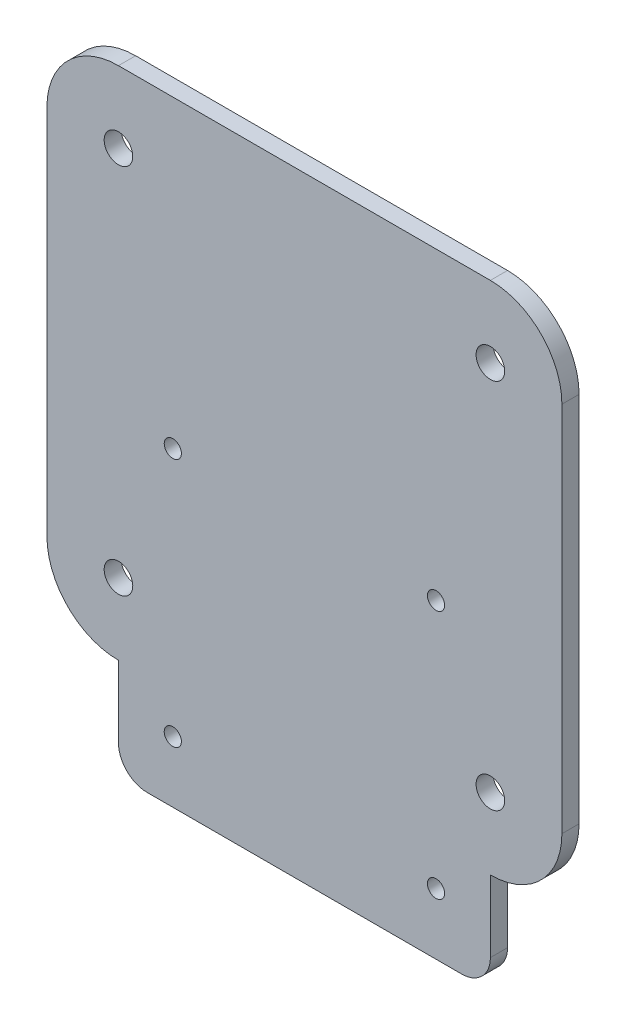
SolidWorks part; units mm, degrees
material "Custom Plastic"
ref_plane "Front Plane" through (0, 0, 0) normal (0, 0, 1) x (1, 0, 0)
ref_plane "Top Plane" through (0, 0, 0) normal (0, 1, 0) x (1, 0, 0)
ref_plane "Right Plane" through (0, 0, 0) normal (1, 0, 0) x (0, 0, -1)
sketch "Sketch1" plane through (0, 0, 0) normal (0, 0, 1) x (1, 0, 0)
  line L1 (-23, -8.2) -> (23, -8.2) construction
  line L2 (-23, -8.2) -> (-23, -51.8) construction
  line L3 (-23, -51.8) -> (23, -51.8) construction
  line L4 (23, -8.2) -> (23, -51.8) construction
  line L5 (-23, -8.2) -> (23, -51.8) construction
  line L6 (-23, -51.8) -> (23, -8.2) construction
  line L7 (-32.5, 45) -> (32.5, 45)
  line L8 (-45, 32.5) -> (-45, -32.5)
  line L9 (-32.5, -45) -> (32.5, -45) construction
  line L10 (45, 32.5) -> (45, -32.5)
  line L11 (-45, 45) -> (45, -45) construction
  line L12 (-45, -45) -> (45, 45) construction
  line L13 (-32.5, 32.5) -> (32.5, 32.5) construction
  line L14 (-32.5, 32.5) -> (-32.5, -32.5) construction
  line L15 (-32.5, -32.5) -> (32.5, -32.5) construction
  line L16 (32.5, 32.5) -> (32.5, -32.5) construction
  line L17 (-32.5, 32.5) -> (32.5, -32.5) construction
  line L18 (-32.5, -32.5) -> (32.5, 32.5) construction
  line L19 (-32.5, -45) -> (32.5, -45) construction
  line L20 (-32.5, -45) -> (-32.5, -57.5)
  line L21 (-27.5, -62.5) -> (27.5, -62.5)
  line L22 (32.5, -45) -> (32.5, -57.5)
  circle A0 centre (-23, -8.2) radius 1.5
  circle A1 centre (23, -8.2) radius 1.5
  circle A2 centre (23, -51.8) radius 1.5
  circle A3 centre (-23, -51.8) radius 1.5
  circle A7 centre (-32.5, 32.5) radius 2.5
  circle A8 centre (32.5, 32.5) radius 2.5
  circle A9 centre (32.5, -32.5) radius 2.5
  circle A10 centre (-32.5, -32.5) radius 2.5
  arc A11 (32.5, -45) -> (45, -32.5) centre (32.5, -32.5) ccw
  arc A12 (-32.5, -45) -> (-45, -32.5) centre (-32.5, -32.5) cw
  arc A13 (45, 32.5) -> (32.5, 45) centre (32.5, 32.5) ccw
  arc A14 (-32.5, 45) -> (-45, 32.5) centre (-32.5, 32.5) ccw
  arc A15 (27.5, -62.5) -> (32.5, -57.5) centre (27.5, -57.5) ccw
  arc A16 (-27.5, -62.5) -> (-32.5, -57.5) centre (-27.5, -57.5) cw
  point P0 (0, 0)
  point P10 (0, 0)
  point P15 (0, 0)
  point P39 (0, -30)
  dimension "D3" = 3
  dimension "D5" = 5
  dimension "D7" = 12.5
  dimension "D10" = 5
  dimension "D1" = 46
  dimension "D2" = 43.6
  dimension "D4" = 12.5
  dimension "D6" = 90
  dimension "D8" = 30
  dimension "D9" = 30
extrude "Boss-Extrude1" add sketch "Sketch1" along normal blind 3
